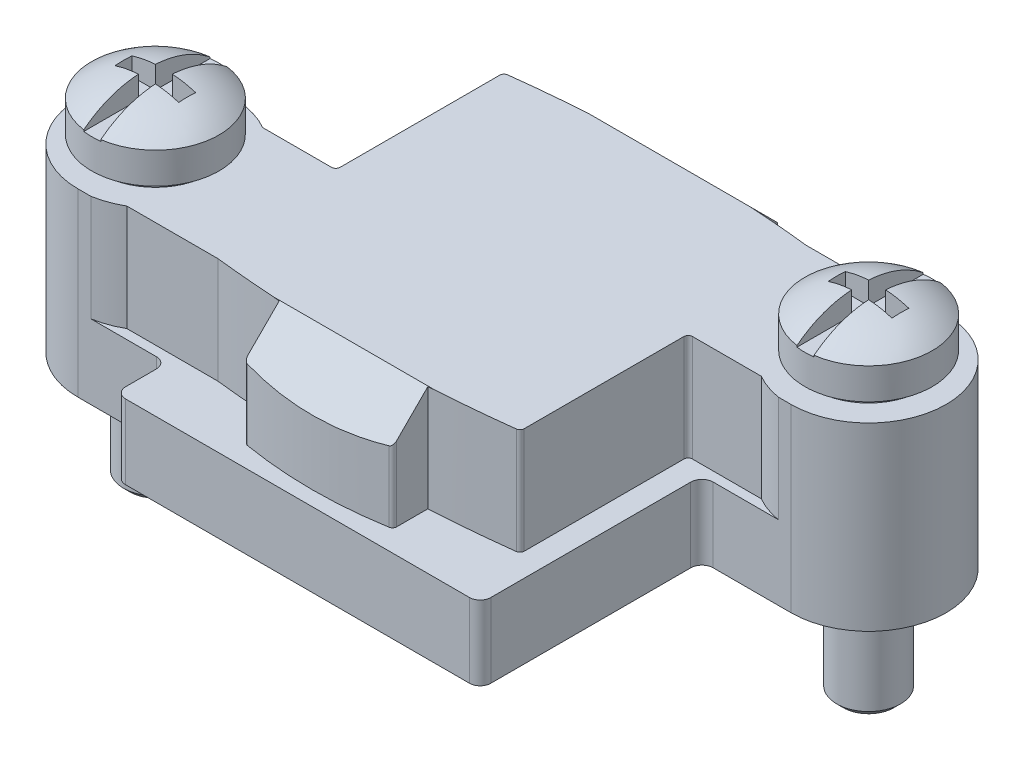
SolidWorks part; units mm, degrees
ref_plane "Front Plane" through (0, 0, 0) normal (0, 0, 1) x (1, 0, 0)
ref_plane "Top Plane" through (0, 0, 0) normal (0, 1, 0) x (1, 0, 0)
ref_plane "Right Plane" through (0, 0, 0) normal (1, 0, 0) x (0, 0, -1)
ref_plane "Plane1" through (0, 0, 0) normal (0, 1, 0) x (1, 0, 0)
sketch "Sketch1" plane through (0, 0, 0) normal (0, 1, 0) x (1, 0, 0)
  line L0 (-12.8, -7.65) -> (-9.1, -7.65)
  line L1 (-8.6, -8.15) -> (-8.6, -9.6)
  line L2 (-8.1, -10.1) -> (8.1, -10.1)
  line L3 (8.6, -9.6) -> (8.6, -0.18)
  line L4 (9.13, 0.35) -> (12.8, 0.35)
  line L5 (12.8, 7.65) -> (9.1, 7.65)
  line L6 (8.6, 8.15) -> (8.6, 9.6)
  line L7 (8.1, 10.1) -> (-8.1, 10.1)
  line L8 (-8.6, 9.6) -> (-8.6, 0.15)
  line L9 (-9.1, -0.35) -> (-12.8, -0.35)
  arc A0 (-12.8, -0.35) -> (-12.8, -7.65) centre (-12.8, -4) ccw
  arc A1 (-9.1, -7.65) -> (-8.6, -8.15) centre (-9.1, -8.15) cw
  arc A2 (-8.6, -9.6) -> (-8.1, -10.1) centre (-8.1, -9.6) ccw
  arc A3 (8.1, -10.1) -> (8.6, -9.6) centre (8.1, -9.6) ccw
  arc A4 (8.6, -0.18) -> (9.13, 0.35) centre (9.13, -0.18) cw
  arc A5 (12.8, 0.35) -> (12.8, 7.65) centre (12.8, 4) ccw
  arc A6 (9.1, 7.65) -> (8.6, 8.15) centre (9.1, 8.15) cw
  arc A7 (8.6, 9.6) -> (8.1, 10.1) centre (8.1, 9.6) ccw
  arc A8 (-8.1, 10.1) -> (-8.6, 9.6) centre (-8.1, 9.6) ccw
  arc A9 (-8.6, 0.15) -> (-9.1, -0.35) centre (-9.1, 0.15) cw
extrude "Boss-Extrude1" add sketch "Sketch1" along normal blind 8.5
ref_plane "Plane2" through (0, 8.5, 0) normal (0, 1, 0) x (1, 0, 0)
sketch "Sketch2" plane through (0, 8.5, 0) normal (0, 1, 0) x (1, 0, 0)
  line L0 (-20.2186, -17.3053) -> (20.3182, -17.3053)
  line L1 (20.3182, -17.3053) -> (20.3182, 15.2137)
  line L2 (20.3182, 15.2137) -> (-20.2186, 15.2137)
  line L3 (-20.2186, 15.2137) -> (-20.2186, -17.3053)
  line L4 (-10.9426, -7.2) -> (-6.6584, -7.2)
  line L5 (-3.5, -7.4684) -> (-3.5, -8.9317)
  line L6 (3.5, -8.9317) -> (3.5, -7.4684)
  line L7 (7.5, -6.9234) -> (7.5, 0.6)
  line L8 (7.7, 0.8) -> (10.9426, 0.8)
  line L9 (10.9426, 7.2) -> (6.6584, 7.2)
  line L10 (3.5, 7.4684) -> (3.5, 8.9317)
  line L11 (-3.5, 8.9317) -> (-3.5, 7.4684)
  line L12 (-7.5, 6.9234) -> (-7.5, -0.6)
  line L13 (-7.7, -0.8) -> (-10.9426, -0.8)
  arc A0 (-10.9426, -0.8) -> (-10.9426, -7.2) centre (-12.8, -4) ccw
  arc A1 (-6.6584, -7.2) -> (-3.5, -7.4684) centre (0, 52.4294) ccw
  arc A2 (-3.5, -8.9317) -> (-3.3333, -9.1289) centre (-3.3, -8.9317) ccw
  arc A3 (-3.3333, -9.1289) -> (3.3333, -9.1289) centre (0, 10.5914) ccw
  arc A4 (3.3333, -9.1289) -> (3.5, -8.9317) centre (3.3, -8.9317) ccw
  arc A5 (3.5, -7.4684) -> (7.3244, -7.1219) centre (0, 52.4294) ccw
  arc A6 (7.3244, -7.1219) -> (7.5, -6.9234) centre (7.3, -6.9234) ccw
  arc A7 (7.5, 0.6) -> (7.7, 0.8) centre (7.7, 0.6) cw
  arc A8 (10.9426, 0.8) -> (10.9426, 7.2) centre (12.8, 4) ccw
  arc A9 (6.6584, 7.2) -> (3.5, 7.4684) centre (0, -52.4294) ccw
  arc A10 (3.5, 8.9317) -> (3.3333, 9.1289) centre (3.3, 8.9317) ccw
  arc A11 (3.3333, 9.1289) -> (-3.3333, 9.1289) centre (0, -10.5914) ccw
  arc A12 (-3.3333, 9.1289) -> (-3.5, 8.9317) centre (-3.3, 8.9317) ccw
  arc A13 (-3.5, 7.4684) -> (-7.3244, 7.1219) centre (0, -52.4294) ccw
  arc A14 (-7.3244, 7.1219) -> (-7.5, 6.9234) centre (-7.3, 6.9234) ccw
  arc A15 (-7.5, -0.6) -> (-7.7, -0.8) centre (-7.7, -0.6) cw
extrude "Cut-Extrude1" cut sketch "Sketch2" against normal blind 5
ref_plane "Plane3" through (0, 0, 0) normal (1, 0, 0) x (0, 0, -1)
sketch "Sketch3" plane through (0, 0, 0) normal (1, 0, 0) x (0, 0, -1)
  line L0 (7.45, 8.5) -> (9.45, 6.5)
  line L1 (9.45, 6.5) -> (9.45, 8.5)
  line L2 (9.45, 8.5) -> (7.45, 8.5)
extrude "Cut-Extrude2" cut sketch "Sketch3" against normal blind 5 and the other way blind 5
ref_plane "Plane4" through (0, 0, 0) normal (1, 0, 0) x (0, 0, -1)
sketch "Sketch4" plane through (0, 0, 0) normal (1, 0, 0) x (0, 0, -1)
  line L0 (-9.45, 6.5) -> (-7.45, 8.5)
  line L1 (-7.45, 8.5) -> (-9.45, 8.5)
  line L2 (-9.45, 8.5) -> (-9.45, 6.5)
extrude "Cut-Extrude3" cut sketch "Sketch4" against normal blind 5 and the other way blind 5
ref_plane "Plane5" through (0, 0, 4) normal (0, 0, 1) x (1, 0, 0)
sketch "Sketch5" plane through (0, 0, 4) normal (0, 0, 1) x (1, 0, 0)
  line L0 (-12.8, 8.5) -> (-15.3, 8.5)
  line L1 (-14.9, 8.9) -> (-12.8, 8.9)
  line L2 (-12.8, 8.9) -> (-12.8, 8.5)
  line L3 (-12.8, 8.9) -> (-12.8, 8.5) construction
  arc A0 (-15.3, 8.5) -> (-14.9, 8.9) centre (-14.9, 8.5) cw
revolve "Revolve1" add sketch "Sketch5" angle 360 about L3
ref_plane "Plane6" through (0, 0, -4) normal (0, 0, 1) x (1, 0, 0)
sketch "Sketch6" plane through (0, 0, -4) normal (0, 0, 1) x (1, 0, 0)
  line L0 (12.8, 8.5) -> (10.3, 8.5)
  line L1 (10.7, 8.9) -> (12.8, 8.9)
  line L2 (12.8, 8.9) -> (12.8, 8.5)
  line L3 (12.8, 8.9) -> (12.8, 8.5) construction
  arc A0 (10.3, 8.5) -> (10.7, 8.9) centre (10.7, 8.5) cw
revolve "Revolve2" add sketch "Sketch6" angle 360 about L3
ref_plane "Plane7" through (0, 0, 4) normal (0, 0, 1) x (1, 0, 0)
sketch "Sketch7" plane through (0, 0, 4) normal (0, 0, 1) x (1, 0, 0)
  line L0 (-12.8, 0) -> (-14.3, 0)
  line L1 (-14.3, 0) -> (-14.3, 4.125)
  line L2 (-14.3, 4.125) -> (-14.175, 4.25)
  line L3 (-14.175, 4.25) -> (-14.3, 4.375)
  line L4 (-14.3, 4.375) -> (-14.3, 8.5)
  line L5 (-14.7, 8.9) -> (-12.8, 8.9)
  line L6 (-12.8, 8.9) -> (-12.8, 0)
  line L7 (-12.8, 8.9) -> (-12.8, 0) construction
  arc A0 (-14.3, 8.5) -> (-14.7, 8.9) centre (-14.7, 8.5) ccw
revolve "Cut-Revolve1" cut sketch "Sketch7" angle 360 about L7
ref_plane "Plane8" through (0, 0, -4) normal (0, 0, 1) x (1, 0, 0)
sketch "Sketch8" plane through (0, 0, -4) normal (0, 0, 1) x (1, 0, 0)
  line L0 (12.8, 0) -> (11.3, 0)
  line L1 (11.3, 0) -> (11.3, 4.125)
  line L2 (11.3, 4.125) -> (11.425, 4.25)
  line L3 (11.425, 4.25) -> (11.3, 4.375)
  line L4 (11.3, 4.375) -> (11.3, 8.5)
  line L5 (10.9, 8.9) -> (12.8, 8.9)
  line L6 (12.8, 8.9) -> (12.8, 0)
  line L7 (12.8, 8.9) -> (12.8, 0) construction
  arc A0 (11.3, 8.5) -> (10.9, 8.9) centre (10.9, 8.5) ccw
revolve "Cut-Revolve2" cut sketch "Sketch8" angle 360 about L7
ref_plane "Plane9" through (0, 0, 4) normal (0, 0, 1) x (1, 0, 0)
sketch "Sketch9" plane through (0, 0, 4) normal (0, 0, 1) x (1, 0, 0)
  line L0 (-12.8, -5.1) -> (-13.9935, -5.1)
  line L1 (-13.9935, -5.1) -> (-14.3, -4.7935)
  line L2 (-14.3, -4.7935) -> (-14.3, 8.9)
  line L3 (-14.3, 8.9) -> (-15.8, 8.9)
  line L4 (-15.8, 8.9) -> (-15.8, 10.37)
  line L5 (-12.8, 11.37) -> (-12.8, -5.1)
  line L6 (-12.8, 11.37) -> (-12.8, -5.1) construction
  arc A0 (-15.8, 10.37) -> (-12.8, 11.37) centre (-12.9361, 6.7782) cw
revolve "Revolve3" add sketch "Sketch9" angle 360 about L6
cosmetic thread "Cosmetic Thread1" parameters "D1"=5.1, "D2"=2.387
ref_plane "Plane10" through (0, 0, -4) normal (0, 0, 1) x (1, 0, 0)
sketch "Sketch10" plane through (0, 0, -4) normal (0, 0, 1) x (1, 0, 0)
  line L0 (12.8, -5.1) -> (11.6065, -5.1)
  line L1 (11.6065, -5.1) -> (11.3, -4.7935)
  line L2 (11.3, -4.7935) -> (11.3, 8.9)
  line L3 (11.3, 8.9) -> (9.8, 8.9)
  line L4 (9.8, 8.9) -> (9.8, 10.37)
  line L5 (12.8, 11.37) -> (12.8, -5.1)
  line L6 (12.8, 11.37) -> (12.8, -5.1) construction
  arc A0 (9.8, 10.37) -> (12.8, 11.37) centre (12.6639, 6.7782) cw
revolve "Revolve4" add sketch "Sketch10" angle 360 about L6
cosmetic thread "Cosmetic Thread2" parameters "D1"=5.1, "D2"=2.387
ref_plane "Plane11" through (0, 10.3, 0) normal (0, 1, 0) x (1, 0, 0)
sketch "Sketch11" plane through (0, 10.3, 0) normal (0, 1, 0) x (1, 0, 0)
  line L0 (11.3, 3.6) -> (12.4, 3.6)
  line L1 (12.4, 3.6) -> (12.4, 1)
  line L2 (12.4, 1) -> (13.2, 1)
  line L3 (13.2, 1) -> (13.2, 3.6)
  line L4 (13.2, 3.6) -> (14.3, 3.6)
  line L5 (14.3, 3.6) -> (14.3, 4.4)
  line L6 (14.3, 4.4) -> (13.2, 4.4)
  line L7 (13.2, 4.4) -> (13.2, 7)
  line L8 (13.2, 7) -> (12.4, 7)
  line L9 (12.4, 7) -> (12.4, 4.4)
  line L10 (12.4, 4.4) -> (11.3, 4.4)
  line L11 (11.3, 4.4) -> (11.3, 3.6)
extrude "Cut-Extrude4" cut sketch "Sketch11" along normal blind 5
ref_plane "Plane12" through (0, 10.3, 0) normal (0, 1, 0) x (1, 0, 0)
sketch "Sketch12" plane through (0, 10.3, 0) normal (0, 1, 0) x (1, 0, 0)
  line L0 (-14.3, -4.4) -> (-13.2, -4.4)
  line L1 (-13.2, -4.4) -> (-13.2, -7)
  line L2 (-13.2, -7) -> (-12.4, -7)
  line L3 (-12.4, -7) -> (-12.4, -4.4)
  line L4 (-12.4, -4.4) -> (-11.3, -4.4)
  line L5 (-11.3, -4.4) -> (-11.3, -3.6)
  line L6 (-11.3, -3.6) -> (-12.4, -3.6)
  line L7 (-12.4, -3.6) -> (-12.4, -1)
  line L8 (-12.4, -1) -> (-13.2, -1)
  line L9 (-13.2, -1) -> (-13.2, -3.6)
  line L10 (-13.2, -3.6) -> (-14.3, -3.6)
  line L11 (-14.3, -3.6) -> (-14.3, -4.4)
extrude "Cut-Extrude5" cut sketch "Sketch12" along normal blind 5
